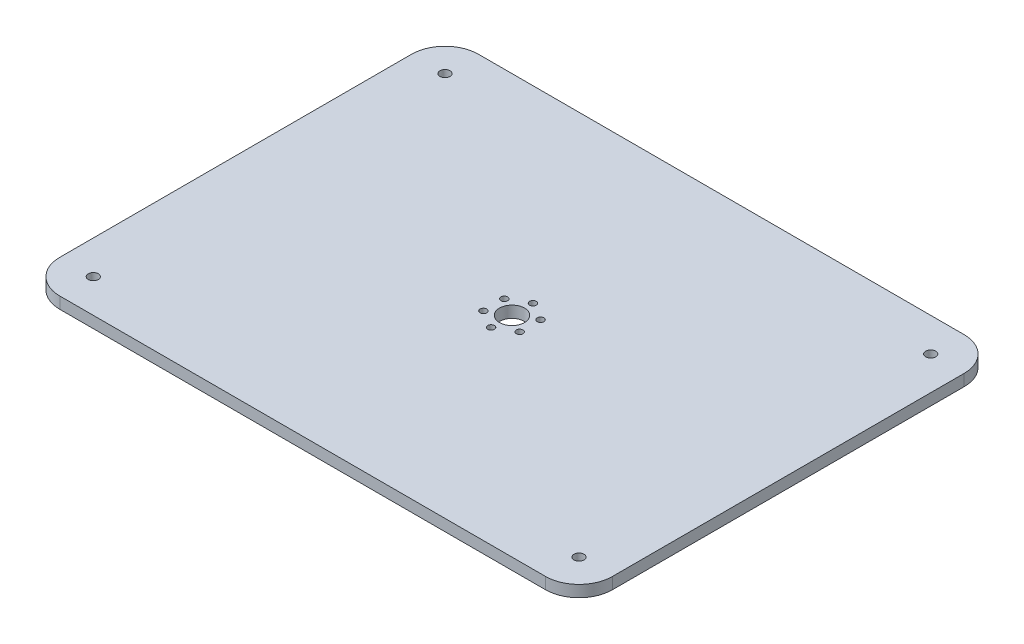
SolidWorks part; units mm, degrees
material "Delrin 2700 NC010, Low Viscosity Acetal Copolymer (SS)"
ref_plane "Front Plane" through (0, 0, 0) normal (0, 0, 1) x (1, 0, 0)
ref_plane "Top Plane" through (0, 0, 0) normal (0, 1, 0) x (1, 0, 0)
ref_plane "Right Plane" through (0, 0, 0) normal (1, 0, 0) x (0, 0, -1)
sketch "Sketch1" plane through (0, 0, 0) normal (0, 1, 0) x (1, 0, 0)
  line L0 (165, 125) -> (-165, -125) construction
  line L5 (-165, -125) -> (165, -125)
  line L6 (-165, -125) -> (-165, 125)
  line L7 (-165, 125) -> (165, 125)
  line L8 (165, -125) -> (165, 125)
  point P5 (0, 0)
  dimension "D1" = 330
  dimension "D2" = 250
extrude "Boss-Extrude1" add sketch "Sketch1" along normal blind 6.9
sketch "Sketch2" plane through (0, 6.9, 0) normal (0, 1, 0) x (1, 0, 0)
  line L0 (145, 105) -> (-145, -105) construction
  line L1 (-145, 105) -> (145, 105) construction
  line L2 (-145, 105) -> (-145, -105) construction
  line L3 (-145, -105) -> (145, -105) construction
  line L4 (145, 105) -> (145, -105) construction
  line L5 (0, 105) -> (0, 125) construction
  line L6 (165, 125) -> (-165, 125) construction
  line L8 (-145, 0) -> (-165, 0) construction
  line L9 (-165, 125) -> (-165, -125) construction
  circle A0 centre (-145, 105) radius 3
  circle A1 centre (145, 105) radius 3
  circle A2 centre (145, -105) radius 3
  circle A3 centre (-145, -105) radius 3
  point P4 (0, 0)
  dimension "D2" = 6
  dimension "D1" = 20
extrude "Cut-Extrude1" cut sketch "Sketch2" against normal through all
sketch "Sketch3" plane through (0, 6.9, 0) normal (0, 1, 0) x (1, 0, 0)
  line L0 (0, 0) -> (0, 12.5) construction
  circle A0 centre (0, 0) radius 12.5 construction
  circle A1 centre (0, 12.5) radius 2
  circle A2 centre (10.8253, 6.25) radius 2
  circle A3 centre (10.8253, -6.25) radius 2
  circle A4 centre (0, -12.5) radius 2
  circle A5 centre (-10.8253, -6.25) radius 2
  circle A6 centre (-10.8253, 6.25) radius 2
  circle A7 centre (0, 0) radius 7.5
  dimension "D3" = 4
  dimension "D4" = 15
  dimension "D2" = 12.5
  dimension "D1" = 6
extrude "Cut-Extrude2" cut sketch "Sketch3" against normal through all
fillet "Fillet1" radius 20 4 edges at (165, 3.45, -125) (-165, 3.45, -125) (-165, 3.45, 125) (165, 3.45, 125)
